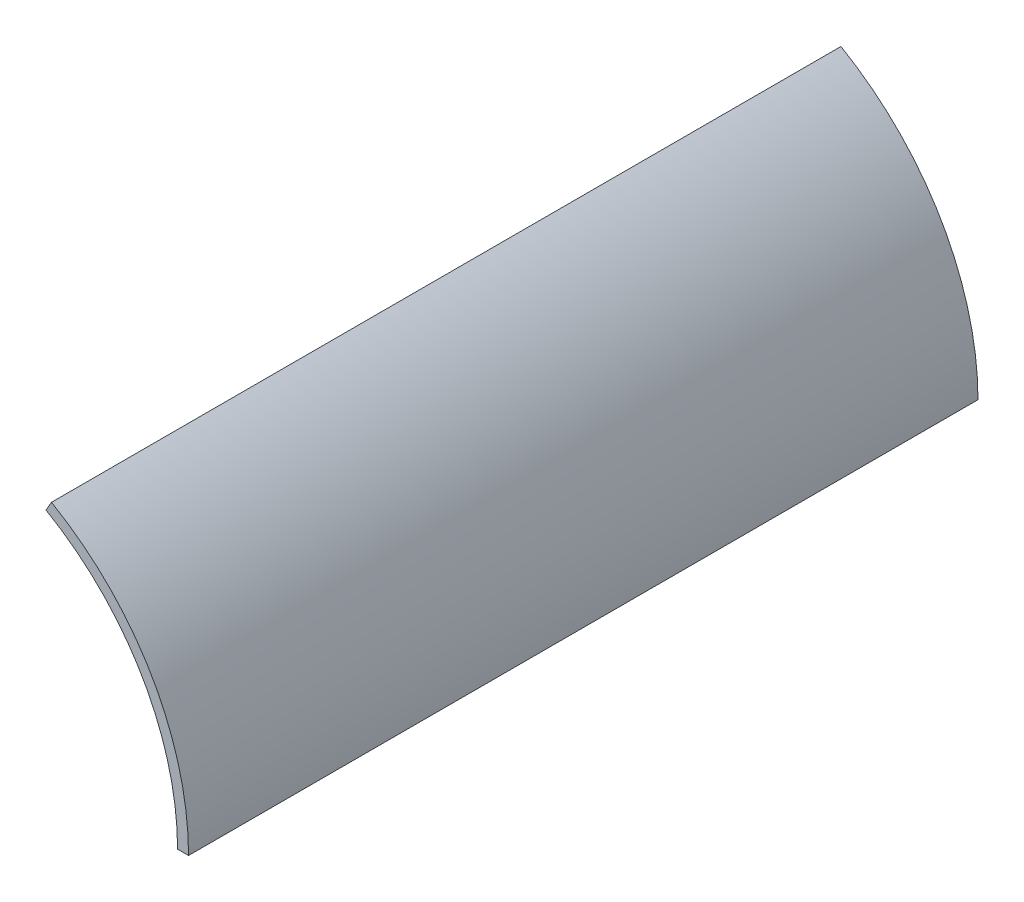
SolidWorks part; units mm, degrees
ref_plane "Front Plane" through (0, 0, 0) normal (0, 0, 1) x (1, 0, 0)
ref_plane "Top Plane" through (0, 0, 0) normal (0, 1, 0) x (1, 0, 0)
ref_plane "Right Plane" through (0, 0, 0) normal (1, 0, 0) x (0, 0, -1)
sketch "Sketch1" plane through (0, 0, 0) normal (0, 0, 1) x (1, 0, 0)
  line L0 (30, 51.9615) -> (31.25, 54.1266)
  line L1 (0, 0) -> (62.5, 0) construction
  line L2 (0, 0) -> (31.25, 54.1266) construction
  line L3 (60, 0) -> (62.5, 0)
  arc A0 (60, 0) -> (30, 51.9615) centre (0, 0) ccw
  arc A1 (62.5, 0) -> (31.25, 54.1266) centre (0, 0) ccw
  dimension "D1" = 120
  dimension "D2" = 125
  dimension "D3" = 60
extrude "Boss-Extrude1" add sketch "Sketch1" along normal blind 120
sketch "Sketch2" plane through (0, 0, 120) normal (0, 0, 1) x (1, 0, 0)
  line L2 (60, 0) -> (62.5, 0)
  line L3 (31.25, 54.1266) -> (30, 51.9615)
  line L4 (60, 0) -> (62.5, 0)
  line L5 (31.25, 54.1266) -> (30, 51.9615)
  arc A2 (60, 0) -> (30, 51.9615) centre (0, 0) ccw
  arc A3 (62.5, 0) -> (31.25, 54.1266) centre (0, 0) ccw
  arc A4 (60, 0) -> (30, 51.9615) centre (0, 0) ccw
  arc A5 (62.5, 0) -> (31.25, 54.1266) centre (0, 0) ccw
  dimension "D1" = 0
extrude "Boss-Extrude2" add sketch "Sketch2" along normal blind 60
